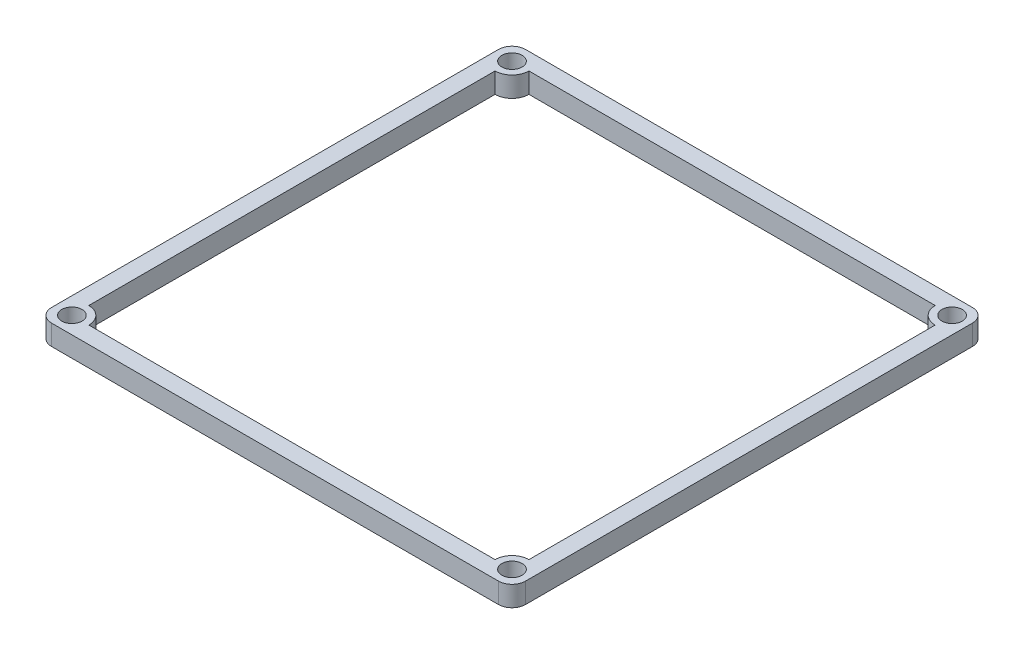
SolidWorks part; units mm, degrees
ref_plane "Front Plane" through (0, 0, 0) normal (0, 0, 1) x (1, 0, 0)
ref_plane "Top Plane" through (0, 0, 0) normal (0, 1, 0) x (1, 0, 0)
ref_plane "Right Plane" through (0, 0, 0) normal (1, 0, 0) x (0, 0, -1)
sketch "Sketch1" plane through (0, 0, 0) normal (0, 1, 0) x (1, 0, 0)
  line L1 (-35, 35) -> (35, 35)
  line L2 (-35, 35) -> (-35, -35)
  line L3 (-35, -35) -> (35, -35)
  line L4 (35, 35) -> (35, -35)
  line L5 (-35, 35) -> (35, -35) construction
  line L6 (-35, -35) -> (35, 35) construction
  circle A0 centre (-32.5, 32.5) radius 1.5
  circle A1 centre (32.5, 32.5) radius 1.5
  circle A2 centre (32.5, -32.5) radius 1.5
  circle A3 centre (-32.5, -32.5) radius 1.5
  point P0 (0, 0)
  dimension "D4" = 3
  dimension "D1" = 70
  dimension "D2" = 70
  dimension "D3" = 2.5
  dimension "D5" = 2
extrude "Boss-Extrude1" add sketch "Sketch1" along normal blind 3
fillet "Fillet1" radius 2 4 edges at (-35, 1.5, -35) (35, 1.5, -35) (35, 1.5, 35) (-35, 1.5, 35)
sketch "Sketch2" plane through (0, 3, 0) normal (0, 1, 0) x (1, 0, 0)
  line L0 (-32.5, -30) -> (-32.5, 30)
  line L1 (-30, 32.5) -> (30, 32.5)
  line L2 (32.5, 30) -> (32.5, -30)
  line L3 (30, -32.5) -> (-30, -32.5)
  circle A0 centre (-32.5, 32.5) radius 2.5 construction
  circle A1 centre (32.5, 32.5) radius 2.5 construction
  circle A2 centre (32.5, -32.5) radius 2.5 construction
  circle A3 centre (-32.5, -32.5) radius 2.5 construction
  arc A4 (-30, -32.5) -> (-32.5, -30) centre (-32.5, -32.5) ccw
  arc A5 (-32.5, 30) -> (-30, 32.5) centre (-32.5, 32.5) ccw
  arc A6 (32.5, 30) -> (30, 32.5) centre (32.5, 32.5) cw
  arc A7 (30, -32.5) -> (32.5, -30) centre (32.5, -32.5) cw
  dimension "D1" = 2
extrude "Cut-Extrude1" cut sketch "Sketch2" against normal through all contours L3 A7 L2 A6 L1 A5 L0 A4
